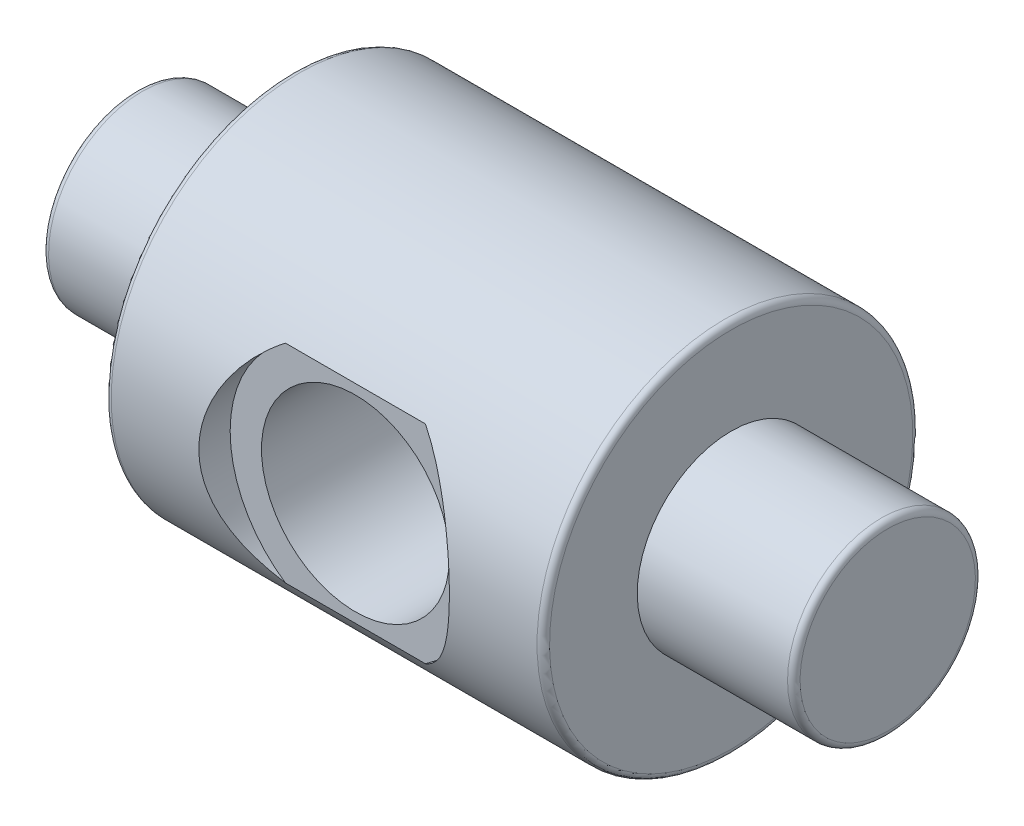
SolidWorks part; units mm, degrees
material "Brass"
ref_plane "Front Plane" through (0, 0, 0) normal (0, 0, 1) x (1, 0, 0)
ref_plane "Top Plane" through (0, 0, 0) normal (0, 1, 0) x (1, 0, 0)
ref_plane "Right Plane" through (0, 0, 0) normal (1, 0, 0) x (0, 0, -1)
sketch "Sketch1" plane through (0, 0, 0) normal (0, 0, 1) x (1, 0, 0)
  line L0 (0, 0) -> (-4.0542, 0)
  line L1 (-4.0542, 0) -> (-4.0542, -1.5)
  line L2 (-4.0542, -1.5) -> (-1.5542, -1.5)
  line L3 (-1.5542, -1.5) -> (-1.5542, -3)
  line L4 (-1.5542, -3) -> (5.4458, -3)
  line L5 (5.4458, -3) -> (5.4458, -1.5)
  line L6 (5.4458, -1.5) -> (7.9458, -1.5)
  line L7 (7.9458, -1.5) -> (7.9458, 0)
  line L8 (7.9458, 0) -> (0, 0)
  dimension "D1" = 1.5
  dimension "D2" = 7
  dimension "D3" = 2.5
  dimension "D4" = 2.5
  dimension "D5" = 1.5
  dimension "D6" = 1.5
revolve "Revolve1" add sketch "Sketch1" angle 360 about L8
fillet "Fillet1" radius 0.1 4 edges at (7.9458, 1.5, 0) (5.4458, 3, 0) (-1.5542, 3, 0) (-4.0542, 1.5, 0)
ref_plane "Plane1" through (0, 0, 3) normal (0, 0, 1) x (1, 0, 0)
sketch "Sketch2" plane through (0, 0, 3) normal (0, 0, 1) x (1, 0, 0)
  line L0 (-1.5542, 1.5) -> (-1.5542, -1.5) construction
  circle A0 centre (1.9458, 0) radius 2
  point P8 (1.9458, 0)
  point P9 (1.9523, -0.013)
  dimension "D1" = 4
  dimension "D2" = 3.5
extrude "Cut-Extrude1" cut sketch "Sketch2" against normal blind 0.5
sketch "Sketch3" plane through (0, 0, 2.5) normal (0, 0, 1) x (1, 0, 0)
  circle A0 centre (1.9458, 0) radius 1.5
  dimension "D1" = 3
extrude "Cut-Extrude2" cut sketch "Sketch3" against normal up to next
